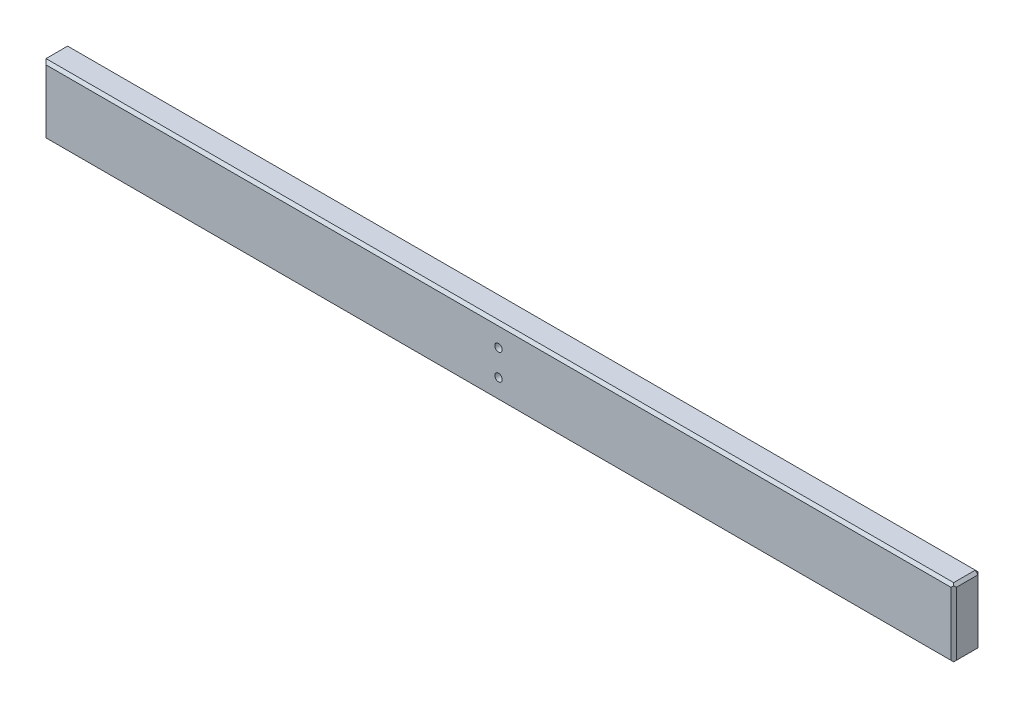
SolidWorks part; units mm, degrees
material "6063-T5"
ref_plane "Alzado" through (0, 0, 0) normal (0, 0, 1) x (1, 0, 0)
ref_plane "Planta" through (0, 0, 0) normal (0, 1, 0) x (1, 0, 0)
ref_plane "Vista lateral" through (0, 0, 0) normal (1, 0, 0) x (0, 0, -1)
sketch "Croquis1" plane through (0, 0, 0) normal (0, 0, 1) x (1, 0, 0)
  line L1 (-336.7, 25.4) -> (336.7, 25.4)
  line L2 (-336.7, 25.4) -> (-336.7, -25.4)
  line L3 (-336.7, -25.4) -> (336.7, -25.4)
  line L4 (336.7, 25.4) -> (336.7, -25.4)
  line L5 (-336.7, 25.4) -> (336.7, -25.4) construction
  line L6 (-336.7, -25.4) -> (336.7, 25.4) construction
  point P0 (0, 0)
  dimension "D1" = 50.8
  dimension "D2" = 673.4
extrude "Saliente-Extruir1" add sketch "Croquis1" along normal blind 20
sketch "Croquis2" plane through (0, 0, 0) normal (0, 0, -1) x (-1, 0, 0)
  line L0 (-336.7, 0) -> (336.7, 0) construction
  line L1 (-336.7, -25.4) -> (-336.7, 25.4) construction
  line L2 (336.7, 25.4) -> (336.7, -25.4) construction
  line L3 (0, 25.4) -> (0, -25.4) construction
  line L4 (-336.7, 25.4) -> (336.7, 25.4) construction
  line L5 (336.7, -25.4) -> (-336.7, -25.4) construction
  circle A0 centre (0, 9.55) radius 2.75
  circle A1 centre (0, -9.55) radius 2.75
  dimension "D1" = 5.5
  dimension "D2" = 19.1
  dimension "D3" = 9.55
extrude "Cortar-Extruir1" cut sketch "Croquis2" against normal through all
chamfer "Chaflán2" distance 2 angle 45 7 edges at (336.7, -25.4, 10) (336.7, 0, 20) (336.7, 25.4, 10) (336.7, 0, 0) (0, -25.4, 0) (-336.7, 0, 0) (0, 25.4, 0)
chamfer "Chaflán5" distance 2 angle 45 3 edges at (-1, 25.4, 20) (-336.7, 0, 20) (-1, -25.4, 20)
